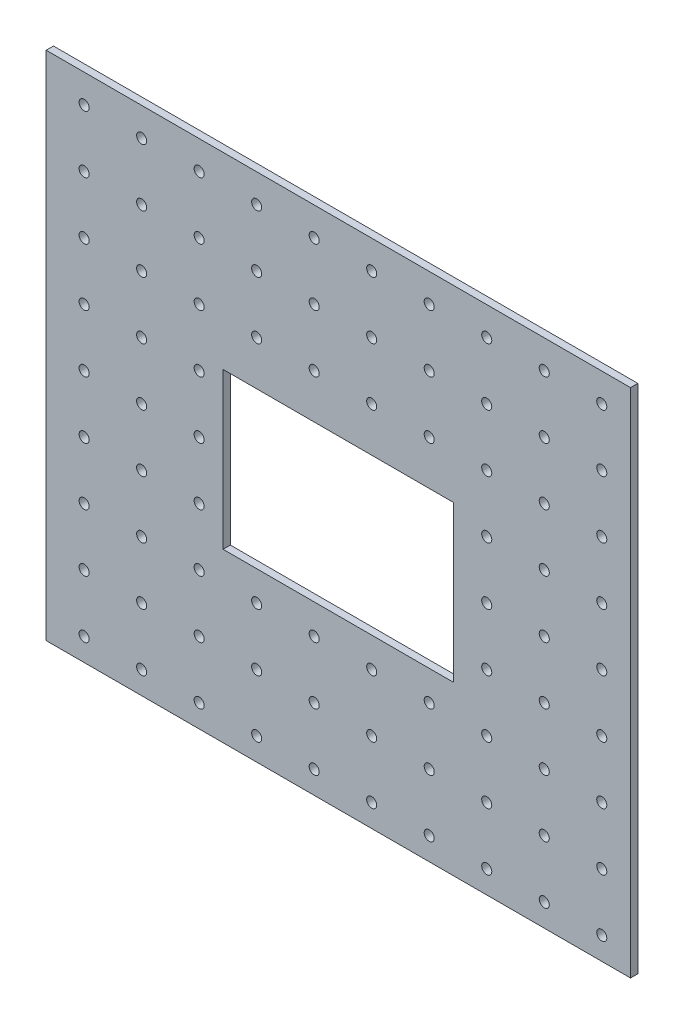
SolidWorks part; units mm, degrees
ref_plane "Front Plane" through (0, 0, 0) normal (0, 0, 1) x (1, 0, 0)
ref_plane "Top Plane" through (0, 0, 0) normal (0, 1, 0) x (1, 0, 0)
ref_plane "Right Plane" through (0, 0, 0) normal (1, 0, 0) x (0, 0, -1)
sketch "Sketch1" plane through (0, 0, 0) normal (0, 0, 1) x (1, 0, 0)
  line L0 (0, 88.9) -> (0, -88.9) construction
  line L1 (-101.6, -88.9) -> (101.6, -88.9)
  line L2 (-101.6, -88.9) -> (-101.6, 88.9)
  line L3 (-101.6, 88.9) -> (101.6, 88.9)
  line L4 (101.6, -88.9) -> (101.6, 88.9)
  line L5 (-101.6, -88.9) -> (101.6, 88.9) construction
  line L6 (-101.6, 88.9) -> (101.6, -88.9) construction
  line L12 (-40.0878, -30.6354) -> (40.0878, -30.6354)
  line L14 (-40.0878, -30.6354) -> (-40.0878, 23.5277)
  line L15 (-40.0878, 23.5277) -> (40.0878, 23.5277)
  line L16 (40.0878, -30.6354) -> (40.0878, 23.5277)
  line L17 (-40.0878, -30.6354) -> (40.0878, 23.5277) construction
  line L18 (-40.0878, 23.5277) -> (40.0878, -30.6354) construction
  point P0 (0, 0)
  point P6 (-23.1, 0)
  point P7 (0, -3.5539)
  point P12 (-101.6, 0)
  point P15 (0, -28.0151)
  point P16 (0, 0)
  point P17 (0, -3.5539)
  dimension "D1" = 177.8
  dimension "D2" = 203.2
  dimension "D3" = 80.1757
extrude "Boss-Extrude1" add sketch "Sketch1" along normal blind 2.54
sketch "Sketch2" plane through (0, 0, 0) normal (0, 0, -1) x (-1, 0, 0)
  line L0 (-101.6, -88.9) -> (-101.6, 88.9) construction
  line L1 (-101.6, 88.9) -> (101.6, 88.9) construction
  circle A0 centre (-91.6, 78.994) radius 1.75
  point P4 (0, 0)
  dimension "D1" = 3.5
  dimension "D2" = 10
  dimension "D3" = 9.906
sketch "Sketch3" plane through (0, 0, 0) normal (0, 0, -1) x (-1, 0, 0)
  point P0 (-91.6, 78.994)
hole_wizard "M2.5 Clearance Hole1" positions "Sketch3" profile "Sketch4" hole size "M2.5" standard "ANSI Metric"
sketch "Sketch4" plane through (91.6, 78.994, 0) normal (1, 0, 0) x (0, 1, 0)
  line L0 (0, 0) -> (0, 5.6235)
  line L1 (0, 5.6235) -> (1.75, 4.572)
  line L2 (1.75, 4.572) -> (1.75, 0)
  line L5 (1.75, 0) -> (0, 0)
  line L10 (0, 5.6235) -> (-1.75, 4.572) construction
  line L11 (0, -6.35) -> (0, 107.95) construction
  dimension "Hole Dia." = 3.5
  dimension "Hole Depth" = 4.572
  dimension "Drill Angle" = 118
pattern_linear "LPattern2" count 9 spacing 20 along (0, -1, 0) count 10 spacing 20 along (-1, 0, 0) skipping (3, 3), (3, 4), (3, 5), (3, 6), (4, 3), (4, 4), (4, 5), (4, 6), (5, 3), (5, 4), (5, 5), (5, 6) of "M2.5 Clearance Hole1"
